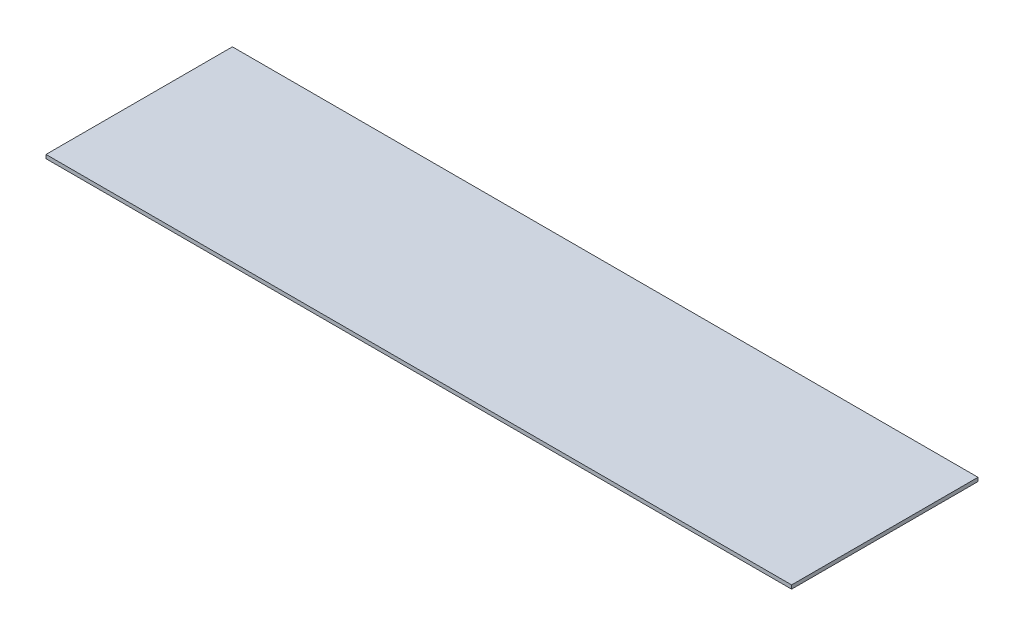
SolidWorks part; units mm, degrees
ref_plane "Front Plane" through (0, 0, 0) normal (0, 0, 1) x (1, 0, 0)
ref_plane "Top Plane" through (0, 0, 0) normal (0, 1, 0) x (1, 0, 0)
ref_plane "Right Plane" through (0, 0, 0) normal (1, 0, 0) x (0, 0, -1)
sketch "Sketch1" plane through (0, 0, 0) normal (0, 1, 0) x (1, 0, 0)
  line L1 (-1000, 250) -> (1000, 250)
  line L2 (-1000, 250) -> (-1000, -250)
  line L3 (-1000, -250) -> (1000, -250)
  line L4 (1000, 250) -> (1000, -250)
  line L5 (-1000, 250) -> (1000, -250) construction
  line L6 (-1000, -250) -> (1000, 250) construction
  point P0 (0, 0)
  dimension "D1" = 500
  dimension "D2" = 2000
extrude "Boss-Extrude1" add sketch "Sketch1" along normal mid plane 10
